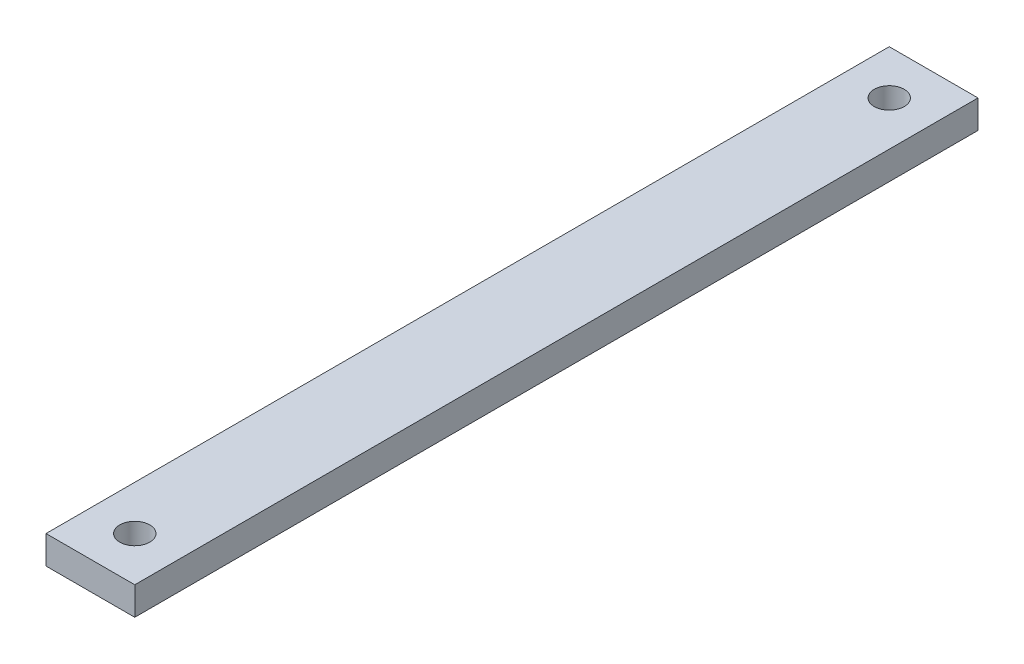
SolidWorks part; units mm, degrees
ref_plane "Front Plane" through (0, 0, 0) normal (0, 0, 1) x (1, 0, 0)
ref_plane "Top Plane" through (0, 0, 0) normal (0, 1, 0) x (1, 0, 0)
ref_plane "Right Plane" through (0, 0, 0) normal (1, 0, 0) x (0, 0, -1)
sketch "Sketch1" plane through (0, 0, 0) normal (0, 1, 0) x (1, 0, 0)
  line L1 (0, 190) -> (20, 190)
  line L2 (0, 190) -> (0, 0)
  line L3 (0, 0) -> (20, 0)
  line L4 (20, 190) -> (20, 0)
  circle A0 centre (10, 10) radius 3.38
  circle A1 centre (10, 180) radius 3.38
  point P9 (0, 0)
  dimension "D3" = 170
  dimension "D4" = 6.76
  dimension "D1" = 190
  dimension "D2" = 20
  dimension "D5" = 10
  dimension "D6" = 10
extrude "Boss-Extrude1" add sketch "Sketch1" along normal blind 6.35
sketch "Sketch2" plane through (0, 6.35, 0) normal (0, 1, 0) x (1, 0, 0)
  line L0 (20, 20) -> (0, 20)
  line L1 (0, 190) -> (0, 0) construction
  line L2 (20, 0) -> (20, 190) construction
  line L3 (0, 170) -> (20, 170)
  line L4 (0, 0) -> (20, 0) construction
  point P2 (0, 0)
  point P5 (0, 0)
  dimension "D1" = 150
  dimension "D2" = 20
